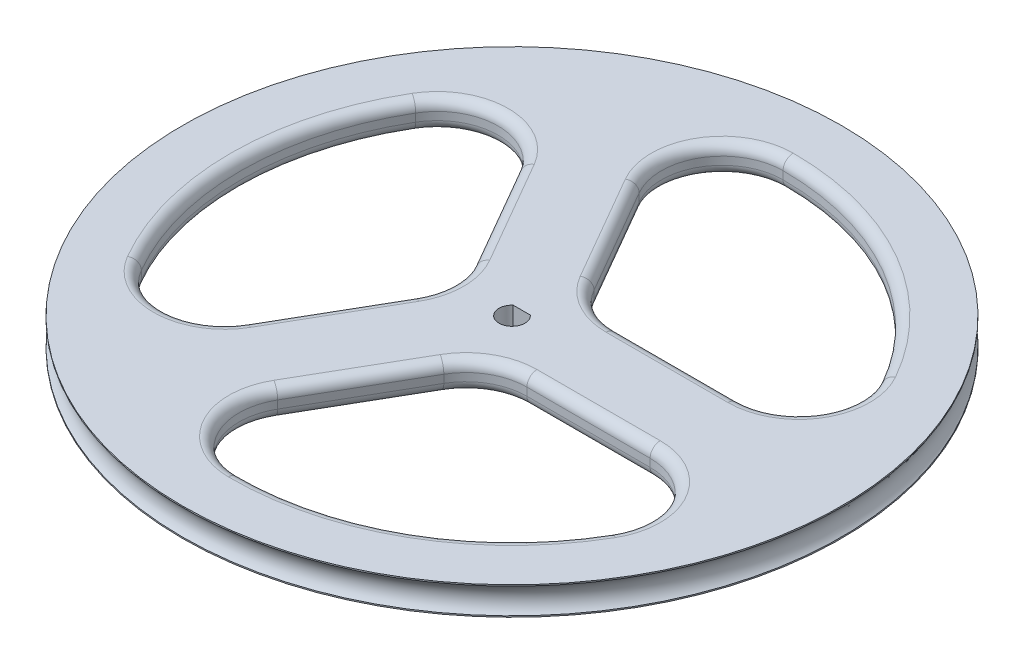
SolidWorks part; units mm, degrees
ref_plane "Front Plane" through (0, 0, 0) normal (0, 0, 1) x (1, 0, 0)
ref_plane "Top Plane" through (0, 0, 0) normal (0, 1, 0) x (1, 0, 0)
ref_plane "Right Plane" through (0, 0, 0) normal (1, 0, 0) x (0, 0, -1)
sketch "Sketch1" plane through (0, 0, 0) normal (0, 1, 0) x (1, 0, 0)
  circle A0 centre (0, 0) radius 41.275
  dimension "D1" = 82.55
extrude "Boss-Extrude1" add sketch "Sketch1" along normal blind 3.5306
sketch "Sketch2" plane through (0, 0, 0) normal (0, 1, 0) x (1, 0, 0)
  line L0 (0.1426, -0.0823) -> (-20.5661, 35.7863)
  line L1 (0.1426, -0.0823) -> (41.2749, -0.0823)
  line L2 (0.1426, -0.0823) -> (20.78, 35.6626) construction
  line L3 (3.294, 5.3759) -> (-15.6524, 38.192) construction
  line L4 (3.294, 5.3759) -> (40.9234, 5.3759) construction
  line L5 (3.294, 5.3759) -> (-11.9639, 31.8034)
  line L6 (3.294, 5.3759) -> (33.5513, 5.3759)
  circle A0 centre (0, 0) radius 41.275 construction
  arc A1 (33.5513, 5.3759) -> (-11.9639, 31.8034) centre (0, 0) ccw
  dimension "D1" = 120
  dimension "D2" = 60
extrude "Cut-Extrude1" cut sketch "Sketch2" along normal blind 3.5306 contours A1 L5 L6
fillet "Fillet2" radius 7.62 3 edges at (3.294, 1.7653, -5.3759) (-11.9639, 1.7653, -31.8034) (33.5513, 1.7653, -5.3759)
fillet "Fillet3" radius 1.27 12 edges at (3.8834, 0, -6.3968) (-2.7634, 0, -15.8676) (-6.6226, 0, -30.1665) (17.0954, 0, -29.3656) (29.5166, 0, -9.1595) (3.8834, 3.5306, -6.3968) (-2.7634, 3.5306, -15.8676) (-6.6226, 3.5306, -30.1665) (17.0954, 3.5306, -29.3656) (29.5166, 3.5306, -9.1595) (15.3131, 0, -5.3759) (15.3131, 3.5306, -5.3759)
pattern_circular "CirPattern3" count 3 over 360 about axis through (0, 0, 0) along (0, 1, 0) of "Cut-Extrude1", "Fillet2", "Fillet3"
sketch "Sketch4" plane through (0, 0, 0) normal (1, 0, 0) x (0, 0, -1)
  line L0 (0, 0) -> (0, 26.6459) construction
  line L1 (38.1, 1.7653) -> (43.7396, 1.7653) construction
  circle A0 centre (42.7997, 1.7653) radius 2.2137
sketch "Sketch5" plane through (0, 0, 0) normal (0, 1, 0) x (1, 0, 0)
  line L0 (-1.0752, 1.2192) -> (1.0752, 1.2192)
  arc A0 (-1.0752, 1.2192) -> (1.0752, 1.2192) centre (0, 0) ccw
  dimension "D1" = 3.2512
  dimension "D2" = 1.2192
extrude "Cut-Extrude2" cut sketch "Sketch5" along normal blind 3.5306
revolve "Cut-Revolve3" cut sketch "Sketch4" angle 360 about L0
